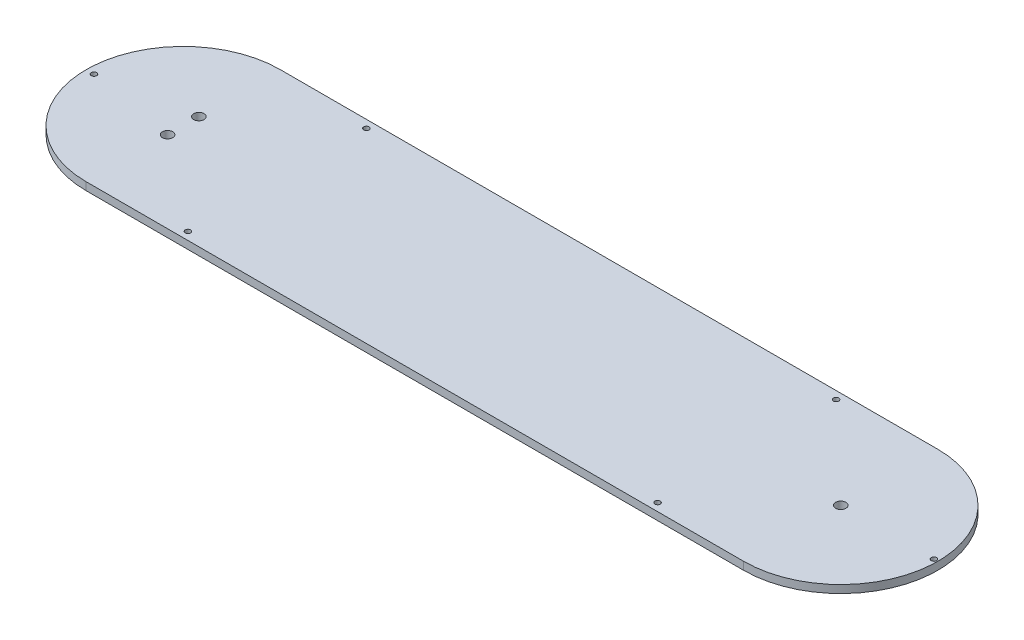
SolidWorks part; units mm, degrees
ref_plane "Front Plane" through (0, 0, 0) normal (0, 0, 1) x (1, 0, 0)
ref_plane "Top Plane" through (0, 0, 0) normal (0, 1, 0) x (1, 0, 0)
ref_plane "Right Plane" through (0, 0, 0) normal (1, 0, 0) x (0, 0, -1)
sketch "Sketch1" plane through (0, 0, 0) normal (0, 1, 0) x (1, 0, 0)
  line L0 (0, 39.37) -> (266.7, 39.37)
  line L1 (0, -39.37) -> (266.7, -39.37)
  line L2 (0, 0) -> (266.7, 0) construction
  arc A0 (0, 39.37) -> (0, -39.37) centre (0, 0) ccw
  arc A1 (266.7, -39.37) -> (266.7, 39.37) centre (266.7, 0) ccw
  circle A2 centre (38.1, 36.195) radius 1.0922
  circle A3 centre (228.6, 36.195) radius 1.0922
  circle A4 centre (38.1, -36.195) radius 1.0922
  circle A5 centre (228.6, -36.195) radius 1.0922
  circle A6 centre (-36.195, 0) radius 1.0922
  circle A7 centre (304.4825, 0) radius 1.0922
  circle A8 centre (266.7, 0) radius 2.1
  circle A9 centre (0, 0) radius 6.35 construction
  circle A10 centre (0, -6.35) radius 2.1
  circle A11 centre (0, 6.35) radius 2.1
  point P27 (0, 0)
  dimension "D1" = 78.74
  dimension "D3" = 4.2
  dimension "D7" = 2.1844
  dimension "D8" = 2.1844
  dimension "D9" = 2.1844
  dimension "D10" = 2.1844
  dimension "D13" = 12.7
  dimension "D14" = 4.2
  dimension "D2" = 266.7
  dimension "D4" = 38.1
  dimension "D5" = 38.1
  dimension "D6" = 3.175
  dimension "D11" = 3.175
  dimension "D12" = 1.5875
  dimension "D15" = 2
extrude "Boss-Extrude1" add sketch "Sketch1" along normal blind 3.175
